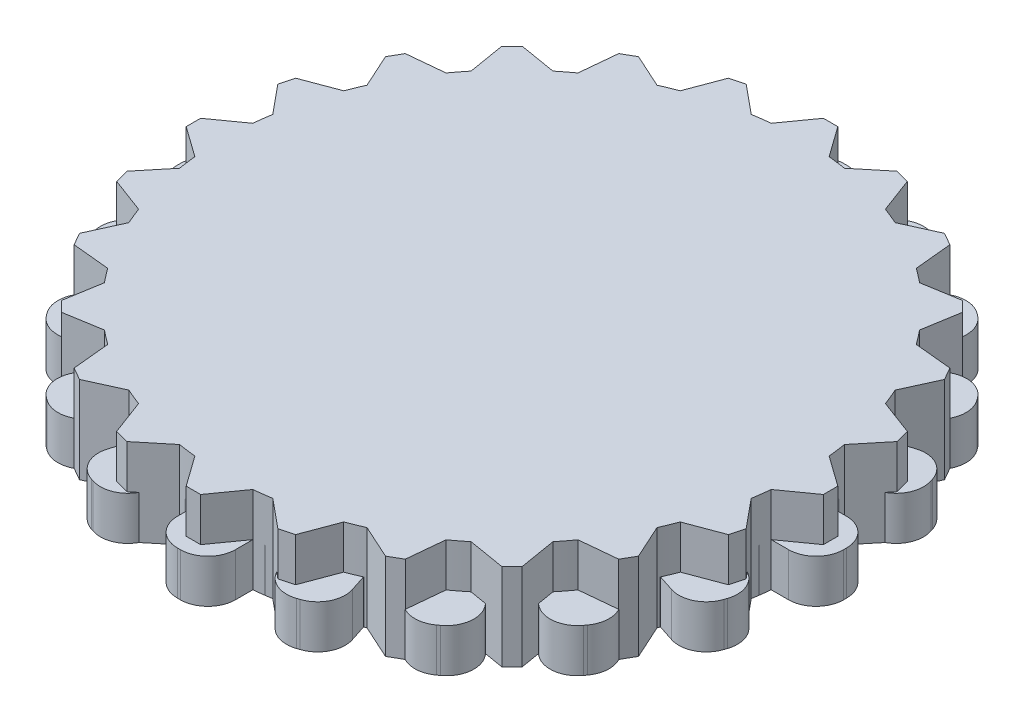
SolidWorks part; units mm, degrees
ref_plane "Front Plane" through (0, 0, 0) normal (0, 0, 1) x (1, 0, 0)
ref_plane "Top Plane" through (0, 0, 0) normal (0, 1, 0) x (1, 0, 0)
ref_plane "Right Plane" through (0, 0, 0) normal (1, 0, 0) x (0, 0, -1)
sketch "Sketch1" plane through (0, 0, 0) normal (0, 1, 0) x (1, 0, 0)
  line L86 (-2.6424, 4.8669) -> (1.3576, 4.8669)
  line L111 (-1.1424, 14.0335) -> (-0.1424, 14.0335)
  line L112 (-0.1424, 14.0335) -> (0.8576, 11.7335)
  line L113 (-1.1424, 14.0335) -> (-2.1424, 11.7335)
  line L114 (5.1239, 12.3544) -> (4.8399, 9.8626)
  line L115 (4.2579, 12.8544) -> (5.1239, 12.3544)
  line L116 (4.2579, 12.8544) -> (2.2419, 11.3626)
  line L117 (8.8451, 8.2672) -> (7.3533, 6.2512)
  line L118 (8.3451, 9.1332) -> (8.8451, 8.2672)
  line L119 (8.3451, 9.1332) -> (5.8533, 8.8492)
  line L120 (10.0242, 2.8669) -> (7.7242, 1.8669)
  line L121 (10.0242, 3.8669) -> (10.0242, 2.8669)
  line L122 (10.0242, 3.8669) -> (7.7242, 4.8669)
  line L123 (8.3451, -2.3994) -> (5.8533, -2.1154)
  line L124 (8.8451, -1.5334) -> (8.3451, -2.3994)
  line L125 (8.8451, -1.5334) -> (7.3533, 0.4826)
  line L126 (4.2579, -6.1207) -> (2.2419, -4.6288)
  line L127 (5.1239, -5.6207) -> (4.2579, -6.1207)
  line L128 (5.1239, -5.6207) -> (4.8399, -3.1288)
  line L129 (-1.1424, -7.2997) -> (-2.1424, -4.9997)
  line L130 (-0.1424, -7.2997) -> (-1.1424, -7.2997)
  line L131 (-0.1424, -7.2997) -> (0.8576, -4.9997)
  line L132 (-6.4087, -5.6207) -> (-6.1247, -3.1288)
  line L133 (-5.5427, -6.1207) -> (-6.4087, -5.6207)
  line L134 (-5.5427, -6.1207) -> (-3.5267, -4.6288)
  line L135 (-10.1299, -1.5334) -> (-8.6381, 0.4826)
  line L136 (-9.6299, -2.3994) -> (-10.1299, -1.5334)
  line L137 (-9.6299, -2.3994) -> (-7.1381, -2.1154)
  line L138 (-11.309, 3.8669) -> (-9.009, 4.8669)
  line L139 (-11.309, 2.8669) -> (-11.309, 3.8669)
  line L140 (-11.309, 2.8669) -> (-9.009, 1.8669)
  line L141 (-9.6299, 9.1332) -> (-7.1381, 8.8492)
  line L142 (-10.1299, 8.2672) -> (-9.6299, 9.1332)
  line L143 (-10.1299, 8.2672) -> (-8.6381, 6.2512)
  line L144 (-5.5427, 12.8544) -> (-3.5267, 11.3626)
  line L145 (-6.4087, 12.3544) -> (-5.5427, 12.8544)
  line L146 (-6.4087, 12.3544) -> (-6.1247, 9.8626)
  line L147 (-2.6424, 1.8669) -> (1.3576, 1.8669)
  line L149 (-3.1424, 4.8669) -> (1.8576, 1.8669) construction
  line L150 (-3.1424, 1.8669) -> (1.8576, 4.8669) construction
  arc A43 (-2.1424, 11.7335) -> (-3.5267, 11.3626) centre (-0.6424, 3.3669) ccw
  arc A44 (-6.1247, 9.8626) -> (-7.1381, 8.8492) centre (-0.6424, 3.3669) ccw
  arc A45 (-8.6381, 6.2512) -> (-9.009, 4.8669) centre (-0.6424, 3.3669) ccw
  arc A46 (-9.009, 1.8669) -> (-8.6381, 0.4826) centre (-0.6424, 3.3669) ccw
  arc A47 (-7.1381, -2.1154) -> (-6.1247, -3.1288) centre (-0.6424, 3.3669) ccw
  arc A48 (-3.5267, -4.6288) -> (-2.1424, -4.9997) centre (-0.6424, 3.3669) ccw
  arc A49 (0.8576, -4.9997) -> (2.2419, -4.6288) centre (-0.6424, 3.3669) ccw
  arc A50 (4.8399, -3.1288) -> (5.8533, -2.1154) centre (-0.6424, 3.3669) ccw
  arc A51 (7.3533, 0.4826) -> (7.7242, 1.8669) centre (-0.6424, 3.3669) ccw
  arc A52 (7.7242, 4.8669) -> (7.3533, 6.2512) centre (-0.6424, 3.3669) ccw
  arc A53 (5.8533, 8.8492) -> (4.8399, 9.8626) centre (-0.6424, 3.3669) ccw
  arc A54 (2.2419, 11.3626) -> (0.8576, 11.7335) centre (-0.6424, 3.3669) ccw
  arc A55 (-2.6424, 4.8669) -> (-2.6424, 1.8669) centre (-0.6424, 3.3669) ccw
  arc A56 (1.3576, 1.8669) -> (1.3576, 4.8669) centre (-0.6424, 3.3669) ccw
  point P6 (0, 0)
  point P8 (0, 0)
  point P9 (0, 0)
  point P12 (0, 2.7462)
  point P17 (0, 0)
  point P18 (0, 2.7462)
  point P22 (-2.5, 0.7462)
  point P63 (0, 0)
  point P68 (0, 0)
  point P69 (-0.6424, 3.3669)
  point P119 (0, 0)
  dimension "D1" = 17
  dimension "D2" = 3
  dimension "D4" = 1
  dimension "D3" = 5
  dimension "D7" = 1
  dimension "2.2" = 2.3
  dimension "1" = 1
  dimension "D9" = 2.3
  dimension "D8" = 12
sketch "Sketch2" plane through (0, 0, 0) normal (0, 1, 0) x (1, 0, 0)
  line L0 (-2, 0) -> (2, 0)
  line L1 (-23, -0.1) -> (-23, 0.1)
  line L2 (-21.1, 2) -> (-19.8997, 2)
  line L3 (-21.1, -2) -> (-19.8997, -2)
  line L4 (-20.6853, 4.6181) -> (-19.5438, 4.2472)
  line L5 (-19.4493, 8.4224) -> (-18.3078, 8.0515)
  line L6 (-21.9052, 7.0123) -> (-21.8434, 7.2025)
  line L7 (-18.2458, 10.7842) -> (-17.2748, 10.0787)
  line L8 (-15.8947, 14.0203) -> (-14.9237, 13.3148)
  line L9 (-18.6662, 13.4382) -> (-18.5486, 13.6)
  line L10 (-14.0203, 15.8947) -> (-13.3148, 14.9237)
  line L11 (-10.7842, 18.2458) -> (-10.0787, 17.2748)
  line L12 (-13.6, 18.5486) -> (-13.4382, 18.6662)
  line L13 (-8.4224, 19.4493) -> (-8.0515, 18.3078)
  line L14 (-4.6181, 20.6853) -> (-4.2472, 19.5438)
  line L15 (-7.2025, 21.8434) -> (-7.0123, 21.9052)
  line L16 (-2, 21.1) -> (-2, 19.8997)
  line L17 (2, 21.1) -> (2, 19.8997)
  line L18 (-0.1, 23) -> (0.1, 23)
  line L19 (4.6181, 20.6853) -> (4.2472, 19.5438)
  line L20 (8.4224, 19.4493) -> (8.0515, 18.3078)
  line L21 (7.0123, 21.9052) -> (7.2025, 21.8434)
  line L22 (10.7842, 18.2458) -> (10.0787, 17.2748)
  line L23 (14.0203, 15.8947) -> (13.3148, 14.9237)
  line L24 (13.4382, 18.6662) -> (13.6, 18.5486)
  line L25 (15.8947, 14.0203) -> (14.9237, 13.3148)
  line L26 (18.2458, 10.7842) -> (17.2748, 10.0787)
  line L27 (18.5486, 13.6) -> (18.6662, 13.4382)
  line L28 (19.4493, 8.4224) -> (18.3078, 8.0515)
  line L29 (20.6853, 4.6181) -> (19.5438, 4.2472)
  line L30 (21.8434, 7.2025) -> (21.9052, 7.0123)
  line L31 (21.1, 2) -> (19.8997, 2)
  line L32 (21.1, -2) -> (19.8997, -2)
  line L33 (23, 0.1) -> (23, -0.1)
  line L34 (20.6853, -4.6181) -> (19.5438, -4.2472)
  line L35 (19.4493, -8.4224) -> (18.3078, -8.0515)
  line L36 (21.9052, -7.0123) -> (21.8434, -7.2025)
  line L37 (18.2458, -10.7842) -> (17.2748, -10.0787)
  line L38 (15.8947, -14.0203) -> (14.9237, -13.3148)
  line L39 (18.6662, -13.4382) -> (18.5486, -13.6)
  line L40 (14.0203, -15.8947) -> (13.3148, -14.9237)
  line L41 (10.7842, -18.2458) -> (10.0787, -17.2748)
  line L42 (13.6, -18.5486) -> (13.4382, -18.6662)
  line L43 (8.4224, -19.4493) -> (8.0515, -18.3078)
  line L44 (4.6181, -20.6853) -> (4.2472, -19.5438)
  line L45 (7.2025, -21.8434) -> (7.0123, -21.9052)
  line L46 (2, -21.1) -> (2, -19.8997)
  line L47 (-2, -21.1) -> (-2, -19.8997)
  line L48 (0.1, -23) -> (-0.1, -23)
  line L49 (-4.6181, -20.6853) -> (-4.2472, -19.5438)
  line L50 (-8.4224, -19.4493) -> (-8.0515, -18.3078)
  line L51 (-7.0123, -21.9052) -> (-7.2025, -21.8434)
  line L52 (-10.7842, -18.2458) -> (-10.0787, -17.2748)
  line L53 (-14.0203, -15.8947) -> (-13.3148, -14.9237)
  line L54 (-13.4382, -18.6662) -> (-13.6, -18.5486)
  line L55 (-15.8947, -14.0203) -> (-14.9237, -13.3148)
  line L56 (-18.2458, -10.7842) -> (-17.2748, -10.0787)
  line L57 (-18.5486, -13.6) -> (-18.6662, -13.4382)
  line L58 (-19.4493, -8.4224) -> (-18.3078, -8.0515)
  line L59 (-20.6853, -4.6181) -> (-19.5438, -4.2472)
  line L60 (-21.8434, -7.2025) -> (-21.9052, -7.0123)
  arc A0 (-18.3078, -8.0515) -> (-17.2748, -10.0787) centre (0, 0) ccw
  arc A1 (-21.1, 2) -> (-23, 0.1) centre (-21.1, 0.1) ccw
  arc A2 (-21.1, -2) -> (-23, -0.1) centre (-21.1, -0.1) cw
  arc A3 (-20.6853, 4.6181) -> (-21.9052, 7.0123) centre (-20.0982, 6.4252) cw
  arc A4 (-19.4493, 8.4224) -> (-21.8434, 7.2025) centre (-20.0364, 6.6154) ccw
  arc A5 (-18.2458, 10.7842) -> (-18.6662, 13.4382) centre (-17.129, 12.3214) cw
  arc A6 (-15.8947, 14.0203) -> (-18.5486, 13.6) centre (-17.0115, 12.4832) ccw
  arc A7 (-14.0203, 15.8947) -> (-13.6, 18.5486) centre (-12.4832, 17.0115) cw
  arc A8 (-10.7842, 18.2458) -> (-13.4382, 18.6662) centre (-12.3214, 17.129) ccw
  arc A9 (-8.4224, 19.4493) -> (-7.2025, 21.8434) centre (-6.6154, 20.0364) cw
  arc A10 (-4.6181, 20.6853) -> (-7.0123, 21.9052) centre (-6.4252, 20.0982) ccw
  arc A11 (-2, 21.1) -> (-0.1, 23) centre (-0.1, 21.1) cw
  arc A12 (2, 21.1) -> (0.1, 23) centre (0.1, 21.1) ccw
  arc A13 (4.6181, 20.6853) -> (7.0123, 21.9052) centre (6.4252, 20.0982) cw
  arc A14 (8.4224, 19.4493) -> (7.2025, 21.8434) centre (6.6154, 20.0364) ccw
  arc A15 (10.7842, 18.2458) -> (13.4382, 18.6662) centre (12.3214, 17.129) cw
  arc A16 (14.0203, 15.8947) -> (13.6, 18.5486) centre (12.4832, 17.0115) ccw
  arc A17 (15.8947, 14.0203) -> (18.5486, 13.6) centre (17.0115, 12.4832) cw
  arc A18 (18.2458, 10.7842) -> (18.6662, 13.4382) centre (17.129, 12.3214) ccw
  arc A19 (19.4493, 8.4224) -> (21.8434, 7.2025) centre (20.0364, 6.6154) cw
  arc A20 (20.6853, 4.6181) -> (21.9052, 7.0123) centre (20.0982, 6.4252) ccw
  arc A21 (21.1, 2) -> (23, 0.1) centre (21.1, 0.1) cw
  arc A22 (21.1, -2) -> (23, -0.1) centre (21.1, -0.1) ccw
  arc A23 (20.6853, -4.6181) -> (21.9052, -7.0123) centre (20.0982, -6.4252) cw
  arc A24 (19.4493, -8.4224) -> (21.8434, -7.2025) centre (20.0364, -6.6154) ccw
  arc A25 (18.2458, -10.7842) -> (18.6662, -13.4382) centre (17.129, -12.3214) cw
  arc A26 (15.8947, -14.0203) -> (18.5486, -13.6) centre (17.0115, -12.4832) ccw
  arc A27 (14.0203, -15.8947) -> (13.6, -18.5486) centre (12.4832, -17.0115) cw
  arc A28 (10.7842, -18.2458) -> (13.4382, -18.6662) centre (12.3214, -17.129) ccw
  arc A29 (8.4224, -19.4493) -> (7.2025, -21.8434) centre (6.6154, -20.0364) cw
  arc A30 (4.6181, -20.6853) -> (7.0123, -21.9052) centre (6.4252, -20.0982) ccw
  arc A31 (2, -21.1) -> (0.1, -23) centre (0.1, -21.1) cw
  arc A32 (-2, -21.1) -> (-0.1, -23) centre (-0.1, -21.1) ccw
  arc A33 (-4.6181, -20.6853) -> (-7.0123, -21.9052) centre (-6.4252, -20.0982) cw
  arc A34 (-8.4224, -19.4493) -> (-7.2025, -21.8434) centre (-6.6154, -20.0364) ccw
  arc A35 (-10.7842, -18.2458) -> (-13.4382, -18.6662) centre (-12.3214, -17.129) cw
  arc A36 (-14.0203, -15.8947) -> (-13.6, -18.5486) centre (-12.4832, -17.0115) ccw
  arc A37 (-15.8947, -14.0203) -> (-18.5486, -13.6) centre (-17.0115, -12.4832) cw
  arc A38 (-18.2458, -10.7842) -> (-18.6662, -13.4382) centre (-17.129, -12.3214) ccw
  arc A39 (-19.4493, -8.4224) -> (-21.8434, -7.2025) centre (-20.0364, -6.6154) cw
  arc A40 (-20.6853, -4.6181) -> (-21.9052, -7.0123) centre (-20.0982, -6.4252) ccw
  arc A41 (-19.8997, -2) -> (-19.5438, -4.2472) centre (0, 0) ccw
  arc A42 (-19.5438, 4.2472) -> (-19.8997, 2) centre (0, 0) ccw
  arc A43 (-17.2748, 10.0787) -> (-18.3078, 8.0515) centre (0, 0) ccw
  arc A44 (-13.3148, 14.9237) -> (-14.9237, 13.3148) centre (0, 0) ccw
  arc A45 (-8.0515, 18.3078) -> (-10.0787, 17.2748) centre (0, 0) ccw
  arc A46 (-2, 19.8997) -> (-4.2472, 19.5438) centre (0, 0) ccw
  arc A47 (4.2472, 19.5438) -> (2, 19.8997) centre (0, 0) ccw
  arc A48 (10.0787, 17.2748) -> (8.0515, 18.3078) centre (0, 0) ccw
  arc A49 (14.9237, 13.3148) -> (13.3148, 14.9237) centre (0, 0) ccw
  arc A50 (18.3078, 8.0515) -> (17.2748, 10.0787) centre (0, 0) ccw
  arc A51 (19.8997, 2) -> (19.5438, 4.2472) centre (0, 0) ccw
  arc A52 (19.5438, -4.2472) -> (19.8997, -2) centre (0, 0) ccw
  arc A53 (17.2748, -10.0787) -> (18.3078, -8.0515) centre (0, 0) ccw
  arc A54 (13.3148, -14.9237) -> (14.9237, -13.3148) centre (0, 0) ccw
  arc A55 (8.0515, -18.3078) -> (10.0787, -17.2748) centre (0, 0) ccw
  arc A56 (2, -19.8997) -> (4.2472, -19.5438) centre (0, 0) ccw
  arc A57 (-10.0787, -17.2748) -> (-8.0515, -18.3078) centre (0, 0) ccw
  arc A58 (-4.2472, -19.5438) -> (-2, -19.8997) centre (0, 0) ccw
  arc A59 (-14.9237, -13.3148) -> (-13.3148, -14.9237) centre (0, 0) ccw
  point P6 (0, 0)
  point P10 (-23, 2)
  point P170 (0, 0)
  dimension "D1" = 40
  dimension "D4" = 1.9
  dimension "D5" = 20
extrude "Boss-Extrude3" add sketch "Sketch2" along normal blind 3
sketch "Sketch3" plane through (0, 0, 0) normal (0, 1, 0) x (1, 0, 0)
  line L0 (-22, 0) -> (22, 0)
  line L1 (22, -0.5) -> (22, 0.5)
  line L2 (22, 0.5) -> (19.8997, 2)
  line L3 (22, -0.5) -> (19.8997, -2)
  line L4 (21.3798, -5.2111) -> (19.7393, -3.2186)
  line L5 (21.121, -6.177) -> (21.3798, -5.2111)
  line L6 (21.121, -6.177) -> (18.704, -7.0823)
  line L7 (19.3026, -10.567) -> (18.2337, -8.2178)
  line L8 (18.8026, -11.433) -> (19.3026, -10.567)
  line L9 (18.8026, -11.433) -> (16.2337, -11.6819)
  line L10 (15.9099, -15.2028) -> (15.4855, -12.657)
  line L11 (15.2028, -15.9099) -> (15.9099, -15.2028)
  line L12 (15.2028, -15.9099) -> (12.657, -15.4855)
  line L13 (11.433, -18.8026) -> (11.6819, -16.2337)
  line L14 (10.567, -19.3026) -> (11.433, -18.8026)
  line L15 (10.567, -19.3026) -> (8.2178, -18.2337)
  line L16 (6.177, -21.121) -> (7.0823, -18.704)
  line L17 (5.2111, -21.3798) -> (6.177, -21.121)
  line L18 (5.2111, -21.3798) -> (3.2186, -19.7393)
  line L19 (0.5, -22) -> (2, -19.8997)
  line L20 (-0.5, -22) -> (0.5, -22)
  line L21 (-0.5, -22) -> (-2, -19.8997)
  line L22 (-5.2111, -21.3798) -> (-3.2186, -19.7393)
  line L23 (-6.177, -21.121) -> (-5.2111, -21.3798)
  line L24 (-6.177, -21.121) -> (-7.0823, -18.704)
  line L25 (-10.567, -19.3026) -> (-8.2178, -18.2337)
  line L26 (-11.433, -18.8026) -> (-10.567, -19.3026)
  line L27 (-11.433, -18.8026) -> (-11.6819, -16.2337)
  line L28 (-15.2028, -15.9099) -> (-12.657, -15.4855)
  line L29 (-15.9099, -15.2028) -> (-15.2028, -15.9099)
  line L30 (-15.9099, -15.2028) -> (-15.4855, -12.657)
  line L31 (-18.8026, -11.433) -> (-16.2337, -11.6819)
  line L32 (-19.3026, -10.567) -> (-18.8026, -11.433)
  line L33 (-19.3026, -10.567) -> (-18.2337, -8.2178)
  line L34 (-21.121, -6.177) -> (-18.704, -7.0823)
  line L35 (-21.3798, -5.2111) -> (-21.121, -6.177)
  line L36 (-21.3798, -5.2111) -> (-19.7393, -3.2186)
  line L37 (-22, -0.5) -> (-19.8997, -2)
  line L38 (-22, 0.5) -> (-22, -0.5)
  line L39 (-22, 0.5) -> (-19.8997, 2)
  line L40 (-21.3798, 5.2111) -> (-19.7393, 3.2186)
  line L41 (-21.121, 6.177) -> (-21.3798, 5.2111)
  line L42 (-21.121, 6.177) -> (-18.704, 7.0823)
  line L43 (-19.3026, 10.567) -> (-18.2337, 8.2178)
  line L44 (-18.8026, 11.433) -> (-19.3026, 10.567)
  line L45 (-18.8026, 11.433) -> (-16.2337, 11.6819)
  line L46 (-15.9099, 15.2028) -> (-15.4855, 12.657)
  line L47 (-15.2028, 15.9099) -> (-15.9099, 15.2028)
  line L48 (-15.2028, 15.9099) -> (-12.657, 15.4855)
  line L49 (-11.433, 18.8026) -> (-11.6819, 16.2337)
  line L50 (-10.567, 19.3026) -> (-11.433, 18.8026)
  line L51 (-10.567, 19.3026) -> (-8.2178, 18.2337)
  line L52 (-6.177, 21.121) -> (-7.0823, 18.704)
  line L53 (-5.2111, 21.3798) -> (-6.177, 21.121)
  line L54 (-5.2111, 21.3798) -> (-3.2186, 19.7393)
  line L55 (-0.5, 22) -> (-2, 19.8997)
  line L56 (0.5, 22) -> (-0.5, 22)
  line L57 (0.5, 22) -> (2, 19.8997)
  line L58 (5.2111, 21.3798) -> (3.2186, 19.7393)
  line L59 (6.177, 21.121) -> (5.2111, 21.3798)
  line L60 (6.177, 21.121) -> (7.0823, 18.704)
  line L61 (10.567, 19.3026) -> (8.2178, 18.2337)
  line L62 (11.433, 18.8026) -> (10.567, 19.3026)
  line L63 (11.433, 18.8026) -> (11.6819, 16.2337)
  line L64 (15.2028, 15.9099) -> (12.657, 15.4855)
  line L65 (15.9099, 15.2028) -> (15.2028, 15.9099)
  line L66 (15.9099, 15.2028) -> (15.4855, 12.657)
  line L67 (18.8026, 11.433) -> (16.2337, 11.6819)
  line L68 (19.3026, 10.567) -> (18.8026, 11.433)
  line L69 (19.3026, 10.567) -> (18.2337, 8.2178)
  line L70 (21.121, 6.177) -> (18.704, 7.0823)
  line L71 (21.3798, 5.2111) -> (21.121, 6.177)
  line L72 (21.3798, 5.2111) -> (19.7393, 3.2186)
  arc A0 (-8.2178, -18.2337) -> (-7.0823, -18.704) centre (0, 0) ccw
  arc A1 (-12.657, -15.4855) -> (-11.6819, -16.2337) centre (0, 0) ccw
  arc A2 (-16.2337, -11.6819) -> (-15.4855, -12.657) centre (0, 0) ccw
  arc A3 (-18.704, -7.0823) -> (-18.2337, -8.2178) centre (0, 0) ccw
  arc A4 (-19.8997, -2) -> (-19.7393, -3.2186) centre (0, 0) ccw
  arc A5 (-19.7393, 3.2186) -> (-19.8997, 2) centre (0, 0) ccw
  arc A6 (-18.2337, 8.2178) -> (-18.704, 7.0823) centre (0, 0) ccw
  arc A7 (-15.4855, 12.657) -> (-16.2337, 11.6819) centre (0, 0) ccw
  arc A8 (-11.6819, 16.2337) -> (-12.657, 15.4855) centre (0, 0) ccw
  arc A9 (-7.0823, 18.704) -> (-8.2178, 18.2337) centre (0, 0) ccw
  arc A10 (-2, 19.8997) -> (-3.2186, 19.7393) centre (0, 0) ccw
  arc A11 (3.2186, 19.7393) -> (2, 19.8997) centre (0, 0) ccw
  arc A12 (8.2178, 18.2337) -> (7.0823, 18.704) centre (0, 0) ccw
  arc A13 (12.657, 15.4855) -> (11.6819, 16.2337) centre (0, 0) ccw
  arc A14 (16.2337, 11.6819) -> (15.4855, 12.657) centre (0, 0) ccw
  arc A15 (18.704, 7.0823) -> (18.2337, 8.2178) centre (0, 0) ccw
  arc A16 (19.8997, 2) -> (19.7393, 3.2186) centre (0, 0) ccw
  arc A17 (19.7393, -3.2186) -> (19.8997, -2) centre (0, 0) ccw
  arc A18 (18.2337, -8.2178) -> (18.704, -7.0823) centre (0, 0) ccw
  arc A19 (-3.2186, -19.7393) -> (-2, -19.8997) centre (0, 0) ccw
  arc A20 (2, -19.8997) -> (3.2186, -19.7393) centre (0, 0) ccw
  arc A21 (7.0823, -18.704) -> (8.2178, -18.2337) centre (0, 0) ccw
  arc A22 (11.6819, -16.2337) -> (12.657, -15.4855) centre (0, 0) ccw
  arc A23 (15.4855, -12.657) -> (16.2337, -11.6819) centre (0, 0) ccw
  point P6 (0, 0)
  point P7 (0, -12.952)
  point P8 (-6.2727, 0)
  point P9 (11.4668, 0)
  point P10 (0, 0)
  point P108 (0, 0)
  dimension "D1" = 40
  dimension "D2" = 22
  dimension "D3" = 2
  dimension "D4" = 24
extrude "Boss-Extrude5" add sketch "Sketch3" along normal blind 6 separate body contours L2 A16 L72 L71 L70 A15 L69 L68 L67 A14 L66 L65 L64 A13 L63 L62 L61 A12 L60 L59 L58 A11 L57 L56 L55 A10 L54 L53 L52 A9 L51 L50 L49 A8 L48 L47 L46 A7 L45 L44 L43 A6 L42 L41 L40 A5 L39 L38 L0 L1 | L10 A23 L9 L8 L7 A18 L6 L5 L4 A17 L3 L1 L0 L38 L37 A4 L36 L35 L34 A3 L33 L32 L31 A2 L30 L29 L28 A1 L27 L26 L25 A0 L24 L23 L22 A19 L21 L20 L19 A20 L18 L17 L16 A21 L15 L14 L13 A22 L12 L11
extrude "Boss-Extrude6" add sketch "Sketch1" along normal blind 6 separate body
sketch "Sketch5" plane through (0, 6, 0) normal (0, 1, 0) x (1, 0, 0)
  line L0 (-0.6424, 14.0335) -> (-0.6424, -7.2997) construction
  line L1 (-0.1424, 14.0335) -> (-1.1424, 14.0335) construction
  line L2 (-1.1424, -7.2997) -> (-0.1424, -7.2997) construction
  line L3 (10.0242, 3.3669) -> (-11.309, 3.3669) construction
  line L4 (10.0242, 2.8669) -> (10.0242, 3.8669) construction
  line L5 (-11.309, 3.8669) -> (-11.309, 2.8669) construction
  circle A0 centre (-0.6424, 3.3669) radius 5.1751
sketch "Sketch6" plane through (0, 6, 0) normal (0, 1, 0) x (1, 0, 0)
  line L36 (-9.8789, 2.8669) -> (-3.0919, 2.8669)
  line L72 (-1.1424, 14.0335) -> (-2.1424, 11.7335)
  line L73 (-3.5267, 11.3626) -> (-5.5427, 12.8544)
  line L74 (-5.5427, 12.8544) -> (-6.4087, 12.3544)
  line L75 (-6.4087, 12.3544) -> (-6.1247, 9.8626)
  line L76 (-7.1381, 8.8492) -> (-9.6299, 9.1332)
  line L77 (-9.6299, 9.1332) -> (-10.1299, 8.2672)
  line L78 (-10.1299, 8.2672) -> (-8.6381, 6.2512)
  line L79 (-9.009, 4.8669) -> (-11.309, 3.8669)
  line L80 (-11.309, 3.8669) -> (-11.309, 2.8669)
  line L81 (-11.309, 2.8669) -> (-9.009, 1.8669)
  line L82 (-8.6381, 0.4826) -> (-10.1299, -1.5334)
  line L83 (-10.1299, -1.5334) -> (-9.6299, -2.3994)
  line L84 (-9.6299, -2.3994) -> (-7.1381, -2.1154)
  line L85 (-6.1247, -3.1288) -> (-6.4087, -5.6207)
  line L86 (-6.4087, -5.6207) -> (-5.5427, -6.1207)
  line L87 (-5.5427, -6.1207) -> (-3.5267, -4.6288)
  line L88 (-2.1424, -4.9997) -> (-1.1424, -7.2997)
  line L89 (-1.1424, -7.2997) -> (-0.1424, -7.2997)
  line L90 (-0.1424, -7.2997) -> (0.8576, -4.9997)
  line L91 (2.2419, -4.6288) -> (4.2579, -6.1207)
  line L92 (4.2579, -6.1207) -> (5.1239, -5.6207)
  line L93 (5.1239, -5.6207) -> (4.8399, -3.1288)
  line L94 (5.8533, -2.1154) -> (8.3451, -2.3994)
  line L95 (8.3451, -2.3994) -> (8.8451, -1.5334)
  line L96 (8.8451, -1.5334) -> (7.3533, 0.4826)
  line L97 (7.7242, 1.8669) -> (10.0242, 2.8669)
  line L98 (10.0242, 2.8669) -> (10.0242, 3.8669)
  line L99 (10.0242, 3.8669) -> (7.7242, 4.8669)
  line L100 (7.3533, 6.2512) -> (8.8451, 8.2672)
  line L101 (8.8451, 8.2672) -> (8.3451, 9.1332)
  line L102 (8.3451, 9.1332) -> (5.8533, 8.8492)
  line L103 (4.8399, 9.8626) -> (5.1239, 12.3544)
  line L104 (5.1239, 12.3544) -> (4.2579, 12.8544)
  line L105 (4.2579, 12.8544) -> (2.2419, 11.3626)
  line L106 (0.8576, 11.7335) -> (-0.1424, 14.0335)
  line L107 (-0.1424, 14.0335) -> (-1.1424, 14.0335)
  line L108 (-1.1424, 14.0335) -> (-2.1424, 11.7335)
  line L109 (-3.5267, 11.3626) -> (-5.5427, 12.8544)
  line L110 (-5.5427, 12.8544) -> (-6.4087, 12.3544)
  line L111 (-6.4087, 12.3544) -> (-6.1247, 9.8626)
  line L112 (-7.1381, 8.8492) -> (-9.6299, 9.1332)
  line L113 (-9.6299, 9.1332) -> (-10.1299, 8.2672)
  line L114 (-10.1299, 8.2672) -> (-8.6381, 6.2512)
  line L115 (-9.009, 4.8669) -> (-11.309, 3.8669)
  line L116 (-11.309, 3.8669) -> (-11.309, 2.8669)
  line L117 (-11.309, 2.8669) -> (-9.009, 1.8669)
  line L118 (-8.6381, 0.4826) -> (-10.1299, -1.5334)
  line L119 (-10.1299, -1.5334) -> (-9.6299, -2.3994)
  line L120 (-9.6299, -2.3994) -> (-7.1381, -2.1154)
  line L121 (-6.1247, -3.1288) -> (-6.4087, -5.6207)
  line L122 (-6.4087, -5.6207) -> (-5.5427, -6.1207)
  line L123 (-5.5427, -6.1207) -> (-3.5267, -4.6288)
  line L124 (-2.1424, -4.9997) -> (-1.1424, -7.2997)
  line L125 (-1.1424, -7.2997) -> (-0.1424, -7.2997)
  line L126 (-0.1424, -7.2997) -> (0.8576, -4.9997)
  line L127 (2.2419, -4.6288) -> (4.2579, -6.1207)
  line L128 (4.2579, -6.1207) -> (5.1239, -5.6207)
  line L129 (5.1239, -5.6207) -> (4.8399, -3.1288)
  line L130 (5.8533, -2.1154) -> (8.3451, -2.3994)
  line L131 (8.3451, -2.3994) -> (8.8451, -1.5334)
  line L132 (8.8451, -1.5334) -> (7.3533, 0.4826)
  line L133 (7.7242, 1.8669) -> (10.0242, 2.8669)
  line L134 (10.0242, 2.8669) -> (10.0242, 3.8669)
  line L135 (10.0242, 3.8669) -> (7.7242, 4.8669)
  line L136 (7.3533, 6.2512) -> (8.8451, 8.2672)
  line L137 (8.8451, 8.2672) -> (8.3451, 9.1332)
  line L138 (8.3451, 9.1332) -> (5.8533, 8.8492)
  line L139 (4.8399, 9.8626) -> (5.1239, 12.3544)
  line L140 (5.1239, 12.3544) -> (4.2579, 12.8544)
  line L141 (4.2579, 12.8544) -> (2.2419, 11.3626)
  line L142 (0.8576, 11.7335) -> (-0.1424, 14.0335)
  line L143 (-0.1424, 14.0335) -> (-1.1424, 14.0335)
  circle A0 centre (-0.6424, 3.3669) radius 9.25
  arc A15 (-2.6424, 4.8669) -> (-2.6424, 1.8669) centre (-0.6424, 3.3669) ccw construction
  arc A27 (-2.1424, 11.7335) -> (-3.5267, 11.3626) centre (-0.6424, 3.3669) ccw
  arc A28 (-6.1247, 9.8626) -> (-7.1381, 8.8492) centre (-0.6424, 3.3669) ccw
  arc A29 (-8.6381, 6.2512) -> (-9.009, 4.8669) centre (-0.6424, 3.3669) ccw
  arc A30 (-9.009, 1.8669) -> (-8.6381, 0.4826) centre (-0.6424, 3.3669) ccw
  arc A31 (-7.1381, -2.1154) -> (-6.1247, -3.1288) centre (-0.6424, 3.3669) ccw
  arc A32 (-3.5267, -4.6288) -> (-2.1424, -4.9997) centre (-0.6424, 3.3669) ccw
  arc A33 (0.8576, -4.9997) -> (2.2419, -4.6288) centre (-0.6424, 3.3669) ccw
  arc A34 (4.8399, -3.1288) -> (5.8533, -2.1154) centre (-0.6424, 3.3669) ccw
  arc A35 (7.3533, 0.4826) -> (7.7242, 1.8669) centre (-0.6424, 3.3669) ccw
  arc A36 (7.7242, 4.8669) -> (7.3533, 6.2512) centre (-0.6424, 3.3669) ccw
  arc A37 (5.8533, 8.8492) -> (4.8399, 9.8626) centre (-0.6424, 3.3669) ccw
  arc A38 (2.2419, 11.3626) -> (0.8576, 11.7335) centre (-0.6424, 3.3669) ccw
  arc A39 (-2.1424, 11.7335) -> (-3.5267, 11.3626) centre (-0.6424, 3.3669) ccw
  arc A40 (-6.1247, 9.8626) -> (-7.1381, 8.8492) centre (-0.6424, 3.3669) ccw
  arc A41 (-8.6381, 6.2512) -> (-9.009, 4.8669) centre (-0.6424, 3.3669) ccw
  arc A42 (-9.009, 1.8669) -> (-8.6381, 0.4826) centre (-0.6424, 3.3669) ccw
  arc A43 (-7.1381, -2.1154) -> (-6.1247, -3.1288) centre (-0.6424, 3.3669) ccw
  arc A44 (-3.5267, -4.6288) -> (-2.1424, -4.9997) centre (-0.6424, 3.3669) ccw
  arc A45 (0.8576, -4.9997) -> (2.2419, -4.6288) centre (-0.6424, 3.3669) ccw
  arc A46 (4.8399, -3.1288) -> (5.8533, -2.1154) centre (-0.6424, 3.3669) ccw
  arc A47 (7.3533, 0.4826) -> (7.7242, 1.8669) centre (-0.6424, 3.3669) ccw
  arc A48 (7.7242, 4.8669) -> (7.3533, 6.2512) centre (-0.6424, 3.3669) ccw
  arc A49 (5.8533, 8.8492) -> (4.8399, 9.8626) centre (-0.6424, 3.3669) ccw
  arc A50 (2.2419, 11.3626) -> (0.8576, 11.7335) centre (-0.6424, 3.3669) ccw
  dimension "D1" = 18.5
  dimension "D3" = 0
